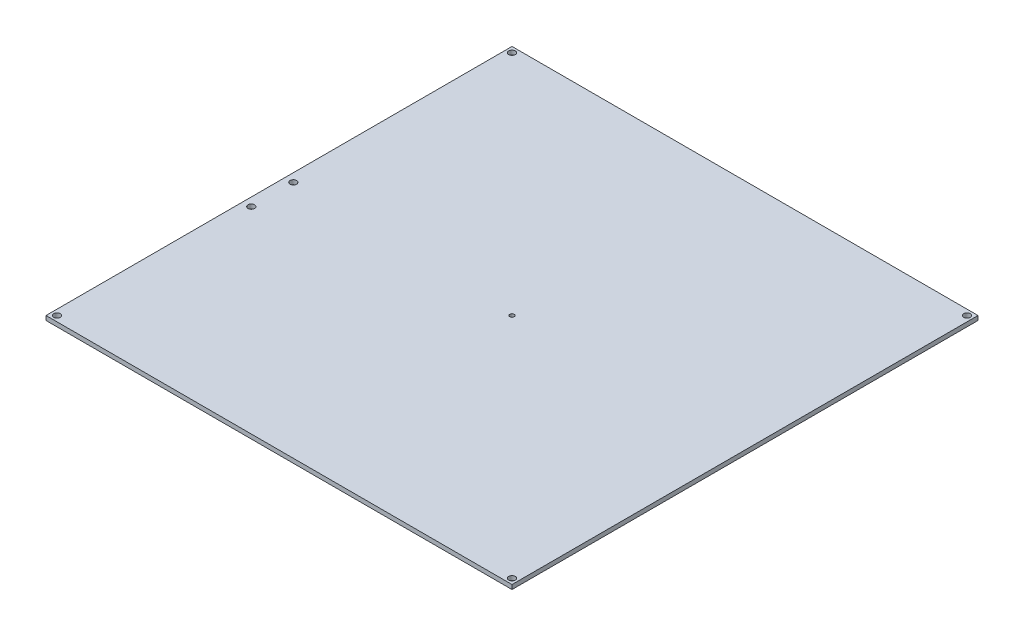
SolidWorks part; units mm, degrees
other "Камера1"
ref_plane "Спереди" through (0, 0, 0) normal (0, 0, 1) x (1, 0, 0)
ref_plane "Сверху" through (0, 0, 0) normal (0, 1, 0) x (1, 0, 0)
ref_plane "Справа" through (0, 0, 0) normal (1, 0, 0) x (0, 0, -1)
sketch "Эскиз1" plane through (0, 0, 0) normal (0, 1, 0) x (1, 0, 0)
  line L1 (-107, -107) -> (107, -107)
  line L2 (-107, -107) -> (-107, 107)
  line L3 (-107, 107) -> (107, 107)
  line L4 (107, -107) -> (107, 107)
  line L5 (-107, -107) -> (107, 107) construction
  line L6 (-107, 107) -> (107, -107) construction
  circle A0 centre (-104.5, 104.5) radius 1.5
  circle A1 centre (104.5, 104.5) radius 1.5
  circle A2 centre (104.5, -104.5) radius 1.5
  circle A3 centre (-104.5, -104.5) radius 1.5
  circle A4 centre (0, 0) radius 1
  point P0 (0, 0)
  point P11 (0, 0)
  point P14 (0, 0)
  point P17 (0, 0)
  point P20 (0, 0)
  dimension "D3" = 104.5
  dimension "D4" = 3
  dimension "D1" = 214
  dimension "D2" = 214
  dimension "D5" = 4
extrude "Бобышка-Вытянуть1" add sketch "Эскиз1" along normal blind 2
sketch "Эскиз4" plane through (0, 2, 0) normal (0, 1, 0) x (1, 0, 0)
  circle A0 centre (-103.1533, 2.7408) radius 1.5
  circle A1 centre (-103.1533, -16.5737) radius 1.5
extrude "Вырез-Вытянуть1" cut sketch "Эскиз4" against normal through all
